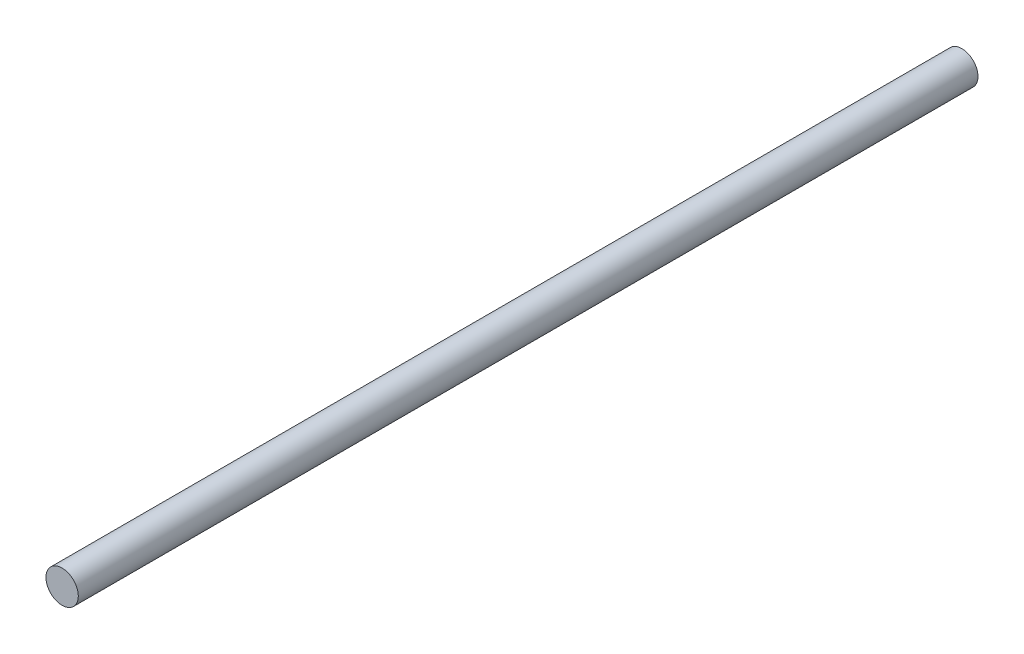
SolidWorks part; units mm, degrees
ref_plane "Plano frontal" through (0, 0, 0) normal (0, 0, 1) x (1, 0, 0)
ref_plane "Plano superior" through (0, 0, 0) normal (0, 1, 0) x (1, 0, 0)
ref_plane "Plano direito" through (0, 0, 0) normal (1, 0, 0) x (0, 0, -1)
sketch "Esboço1" plane through (0, 0, 0) normal (0, 0, 1) x (1, 0, 0)
  circle A0 centre (0, 0) radius 6
  dimension "D1" = 12
extrude "Ressalto-extrusão1" add sketch "Esboço1" along normal blind 334
